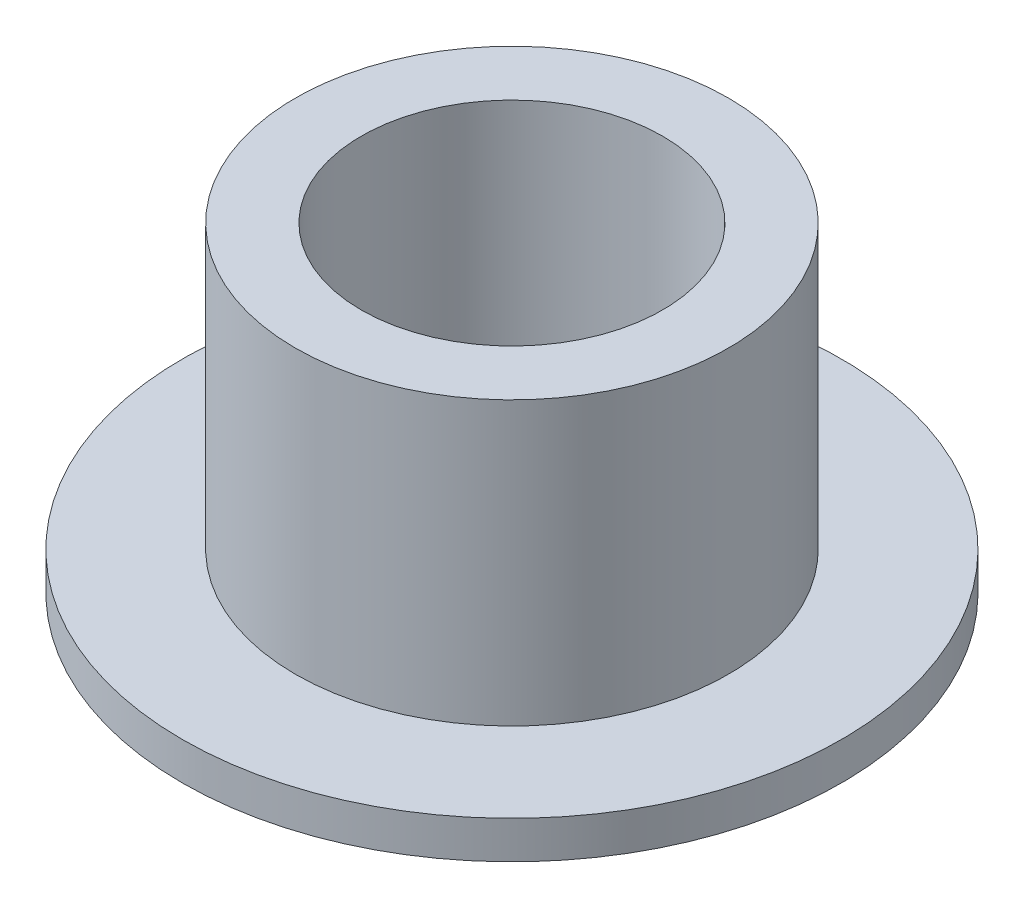
SolidWorks part; units mm, degrees
ref_plane "Front Plane" through (0, 0, 0) normal (0, 0, 1) x (1, 0, 0)
ref_plane "Top Plane" through (0, 0, 0) normal (0, 1, 0) x (1, 0, 0)
ref_plane "Right Plane" through (0, 0, 0) normal (1, 0, 0) x (0, 0, -1)
sketch "Sketch1" plane through (0, 0, 0) normal (0, 1, 0) x (1, 0, 0)
  circle A0 centre (0, 0) radius 3.5
  dimension "D1" = 7
extrude "Boss-Extrude1" add sketch "Sketch1" along normal blind 0.4
sketch "Sketch2" plane through (0, 0.4, 0) normal (0, 1, 0) x (1, 0, 0)
  circle A0 centre (0, 0) radius 2.3
  dimension "D1" = 4.6
extrude "Boss-Extrude2" add sketch "Sketch2" along normal blind 3
sketch "Sketch3" plane through (0, 3.4, 0) normal (0, 1, 0) x (1, 0, 0)
  circle A0 centre (0, 0) radius 1.6
  dimension "D1" = 3.2
extrude "Cut-Extrude1" cut sketch "Sketch3" against normal blind 16
